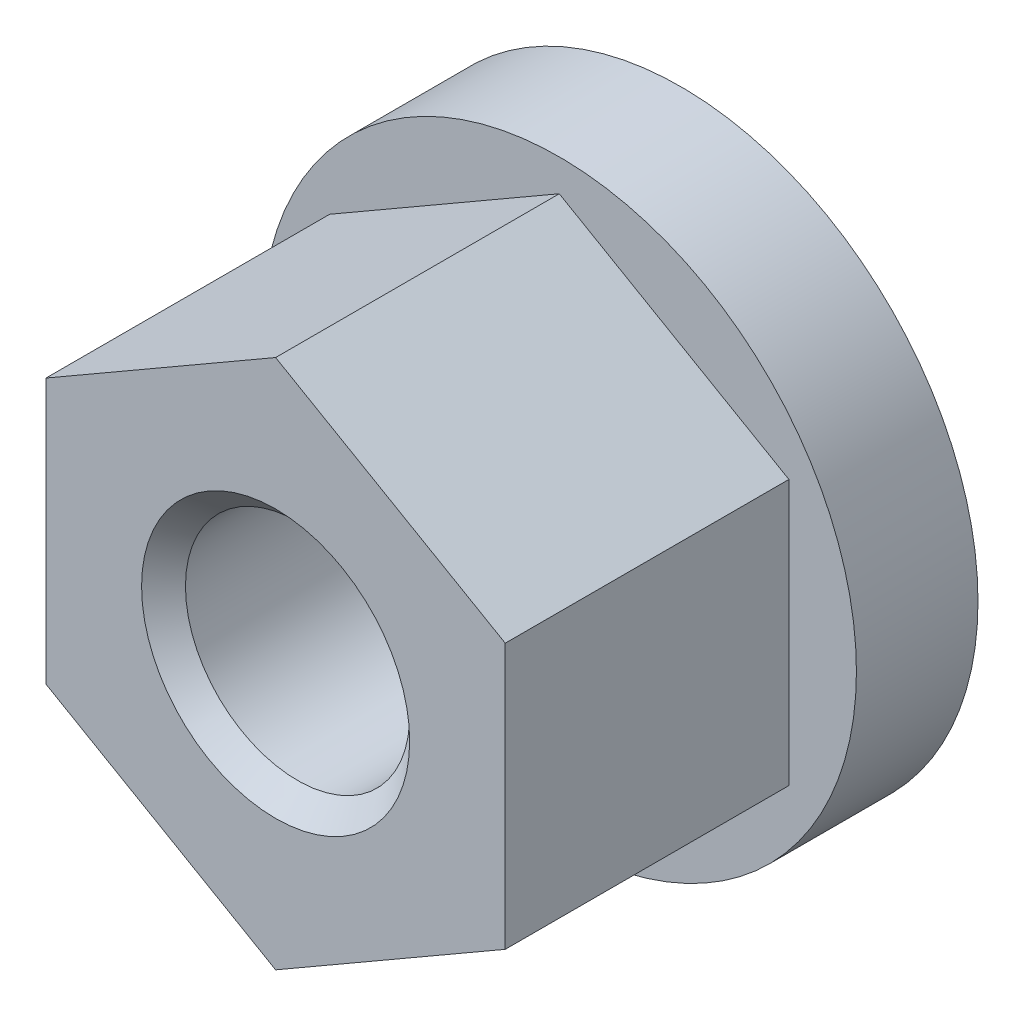
SolidWorks part; units mm, degrees
ref_plane "前基準面" through (0, 0, 0) normal (0, 0, 1) x (1, 0, 0)
ref_plane "上基準面" through (0, 0, 0) normal (0, 1, 0) x (1, 0, 0)
ref_plane "右基準面" through (0, 0, 0) normal (1, 0, 0) x (0, 0, -1)
sketch "草圖1" plane through (0, 0, 0) normal (0, 1, 0) x (1, 0, 0)
  line L0 (11, 15) -> (0, 15)
  line L1 (0, 15) -> (0, 10.5)
  line L2 (0, 10.5) -> (11, 10.5)
  line L3 (11, 10.5) -> (11, 15)
  line L4 (0, 15) -> (0, 10.5) construction
revolve "旋轉1" add sketch "草圖1" angle 360 about L4
sketch "草圖2" plane through (0, 0, -10.5) normal (0, 0, 1) x (1, 0, 0)
  line L0 (-8.5, -4.9075) -> (-8.5, 4.9075)
  line L1 (-8.5, 4.9075) -> (0, 9.815)
  line L2 (0, 9.815) -> (8.5, 4.9075)
  line L3 (8.5, 4.9075) -> (8.5, -4.9075)
  line L4 (8.5, -4.9075) -> (0, -9.815)
  line L5 (0, -9.815) -> (-8.5, -4.9075)
extrude "填料-伸長1" add sketch "草圖2" along normal blind 10.5
hole_wizard "鑽孔1" positions "草圖4" profile "草圖3" legacy
sketch "草圖4" plane through (0, 0, 0) normal (0, 0, 1) x (1, 0, 0)
  point P0 (0, 0)
sketch "草圖3" plane through (0, 0, 0) normal (1, 0, 0) x (0, -1, 0)
  line L0 (0, 0) -> (0, 15)
  line L1 (0, 15) -> (4.15, 15)
  line L2 (4.15, 15) -> (4.15, 0)
  line L3 (4.15, 0) -> (0, 0)
  line L4 (0, 110) -> (0, -10) construction
  dimension "直徑" = 8.3
  dimension "深度" = 15
chamfer "導角1" distance 0.812 angle 45 2 edges at (4.15, 0, -15) (4.15, 0, 0)
